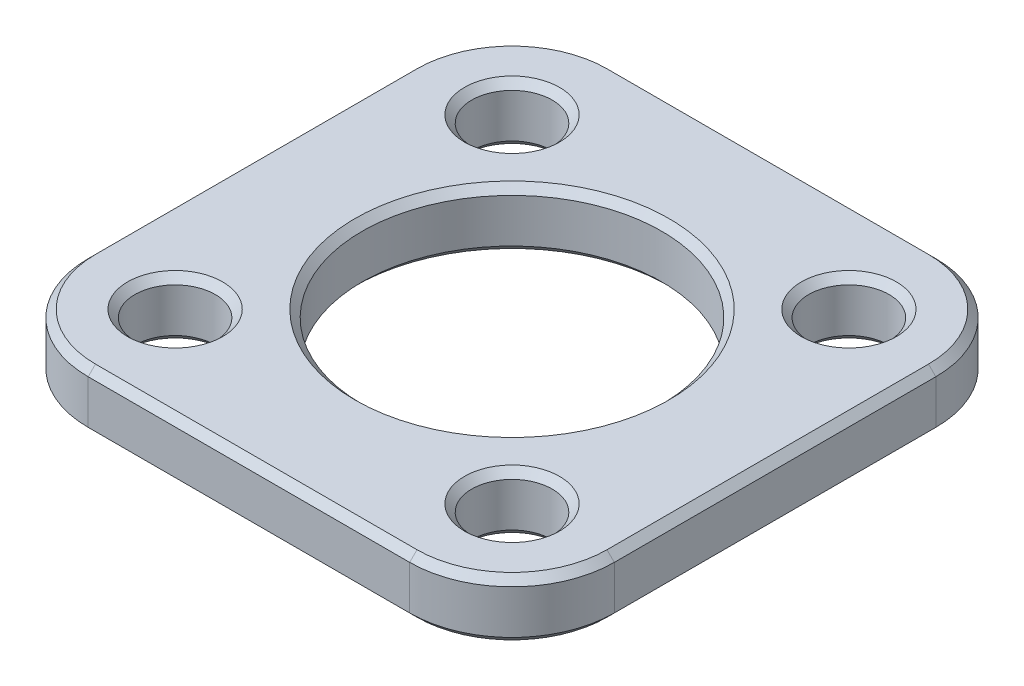
SolidWorks part; units mm, degrees
material "A-Glasfaser"
ref_plane "Front Plane" through (0, 0, 0) normal (0, 0, 1) x (1, 0, 0)
ref_plane "Top Plane" through (0, 0, 0) normal (0, 1, 0) x (1, 0, 0)
ref_plane "Right Plane" through (0, 0, 0) normal (1, 0, 0) x (0, 0, -1)
sketch "Sketch1" plane through (0, 0, 0) normal (0, 1, 0) x (1, 0, 0)
  line L0 (-11.5258, 11.5258) -> (11.5258, -11.5258) construction
  line L1 (-11.5258, 11.5258) -> (11.5258, 11.5258) construction
  line L2 (-11.5258, 11.5258) -> (-11.5258, -11.5258) construction
  line L3 (-11.5258, -11.5258) -> (11.5258, -11.5258) construction
  line L4 (11.5258, 11.5258) -> (11.5258, -11.5258) construction
  line L6 (-11, 18) -> (11, 18)
  line L7 (-18, 11) -> (-18, -11)
  line L8 (-11, -18) -> (11, -18)
  line L9 (18, 11) -> (18, -11)
  line L10 (-18, 18) -> (18, -18) construction
  line L11 (-18, -18) -> (18, 18) construction
  circle A0 centre (0, 0) radius 10.25
  circle A1 centre (-11.5258, 11.5258) radius 2.75
  circle A2 centre (11.5258, 11.5258) radius 2.75
  circle A3 centre (11.5258, -11.5258) radius 2.75
  circle A4 centre (-11.5258, -11.5258) radius 2.75
  arc A5 (-18, -11) -> (-11, -18) centre (-11, -11) ccw
  arc A6 (11, -18) -> (18, -11) centre (11, -11) ccw
  arc A7 (11, 18) -> (18, 11) centre (11, 11) cw
  arc A8 (-11, 18) -> (-18, 11) centre (-11, 11) ccw
  dimension "D2" = 20.5
  dimension "D3" = 5.5
  dimension "D4" = 36
  dimension "D5" = 7
  dimension "D1" = 32.6
extrude "Boss-Extrude1" add sketch "Sketch1" along normal blind 4
chamfer "Chamfer1" distance 0.5 angle 45 26 edges at (-11.5258, 0, 14.2758) (11.5258, 0, 14.2758) (11.5258, 0, -8.7758) (-11.5258, 0, -8.7758) (0, 0, 10.25) (-11.5258, 4, 14.2758) (11.5258, 4, -8.7758) (0, 4, 10.25) (-11.5258, 4, -8.7758) (11.5258, 4, 14.2758) (-15.9497, 0, 15.9497) (18, 0, 0) (-15.9497, 4, 15.9497) (18, 4, 0) (0, 0, 18) (15.9497, 0, 15.9497) (15.9497, 0, -15.9497) (0, 0, -18) (-15.9497, 0, -15.9497) (-18, 0, 0) (-18, 4, 0) (-15.9497, 4, -15.9497) (0, 4, -18) (15.9497, 4, -15.9497) (15.9497, 4, 15.9497) (0, 4, 18)
